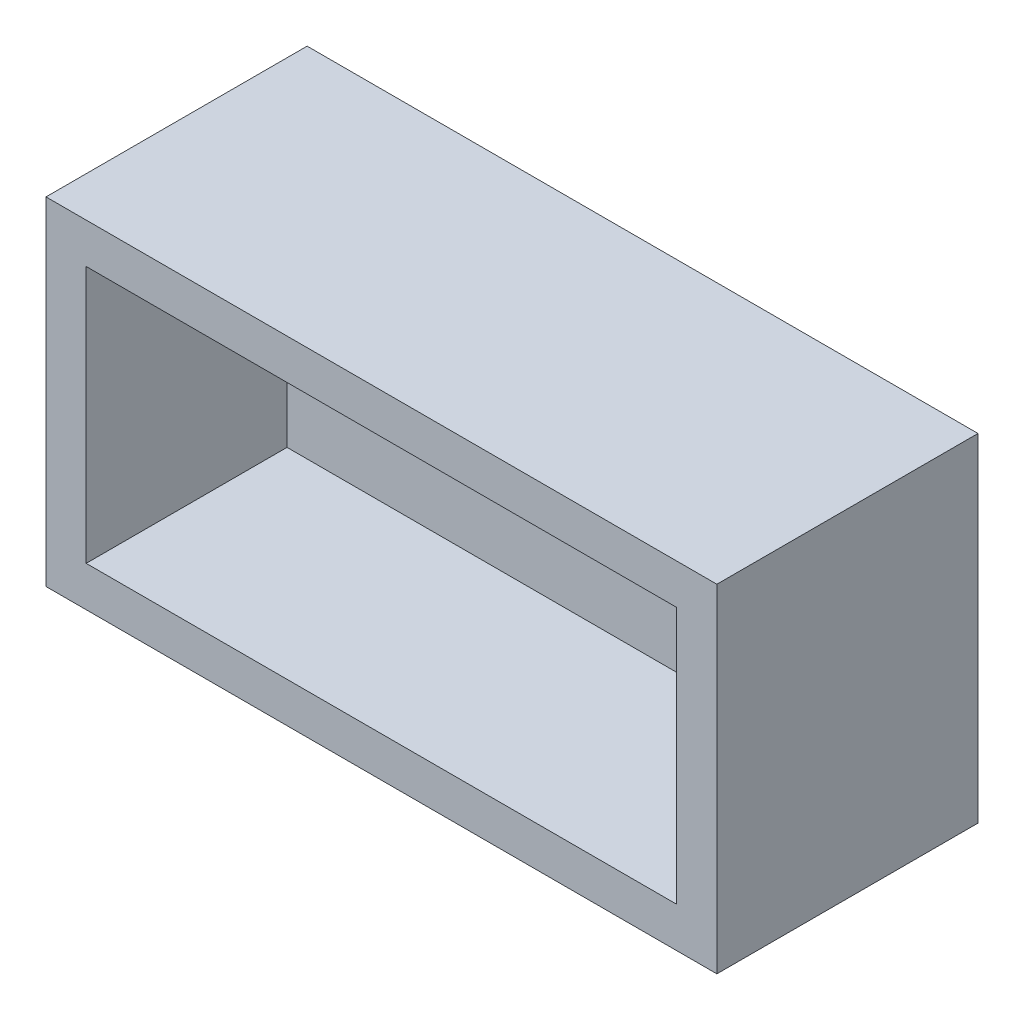
SolidWorks part; units mm, degrees
ref_plane "Спереди" through (0, 0, 0) normal (0, 0, 1) x (1, 0, 0)
ref_plane "Сверху" through (0, 0, 0) normal (0, 1, 0) x (1, 0, 0)
ref_plane "Справа" through (0, 0, 0) normal (1, 0, 0) x (0, 0, -1)
sketch "Эскиз2" plane through (0, 0, 0) normal (0, 0, 1) x (1, 0, 0)
  line L1 (-16.7, -8.4) -> (16.7, -8.4)
  line L2 (-16.7, -8.4) -> (-16.7, 8.4)
  line L3 (-16.7, 8.4) -> (16.7, 8.4)
  line L4 (16.7, -8.4) -> (16.7, 8.4)
  line L5 (-16.7, -8.4) -> (16.7, 8.4) construction
  line L6 (-16.7, 8.4) -> (16.7, -8.4) construction
  point P0 (0, 0)
  dimension "D1" = 33.4
  dimension "D2" = 16.8
extrude "Бобышка-Вытянуть1" add sketch "Эскиз2" along normal blind 13
sketch "Эскиз3" plane through (0, 0, 13) normal (0, 0, 1) x (1, 0, 0)
  line L0 (-16.7, 8.4) -> (-16.7, -8.4) construction
  line L1 (-14.7, 6.4) -> (14.7, 6.4)
  line L2 (-14.7, 6.4) -> (-14.7, -6.4)
  line L3 (-14.7, -6.4) -> (14.7, -6.4)
  line L4 (14.7, 6.4) -> (14.7, -6.4)
  line L5 (16.7, 8.4) -> (-16.7, 8.4) construction
  line L6 (-16.7, -8.4) -> (16.7, -8.4) construction
  dimension "D1" = 29.4
  dimension "D2" = 2
  dimension "D3" = 2
  dimension "D4" = 2
extrude "Вырез-Вытянуть1" cut sketch "Эскиз3" against normal blind 10
